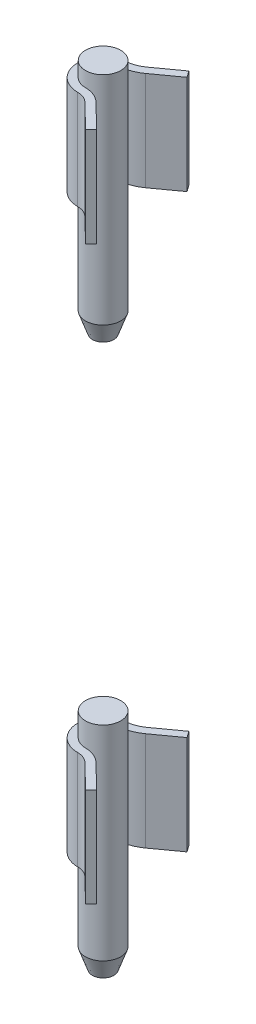
SolidWorks part; units mm, degrees
ref_plane "Front Plane" through (0, 0, 0) normal (0, 0, 1) x (1, 0, 0)
ref_plane "Top Plane" through (0, 0, 0) normal (0, 1, 0) x (1, 0, 0)
ref_plane "Right Plane" through (0, 0, 0) normal (1, 0, 0) x (0, 0, -1)
sketch "Sketch1" plane through (0, 0, 0) normal (0, 1, 0) x (1, 0, 0)
  circle A0 centre (0, 0) radius 4.5
  dimension "D1" = 9
extrude "Boss-Extrude1" add sketch "Sketch1" along normal blind 55
chamfer "Chamfer1" distance 1.75 distance2 5 1 edges at (0, 0, 4.5)
ref_plane "Plane1" through (0, 73, 0) normal (0, -1, 0) x (-1, 0, 0)
ref_plane "Plane2" through (0, 25.9, 0) normal (0, -1, 0) x (-1, 0, 0)
sketch "Sketch2" plane through (0, 25.9, 0) normal (0, -1, 0) x (-1, 0, 0)
  line L0 (-10.6679, -12.3261) -> (-4.5, -6.3274)
  line L2 (-9.2735, -13.7598) -> (-3.1056, -7.7611)
  line L4 (-9.2735, -13.7598) -> (-10.6679, -12.3261)
  line L7 (-3.3302, 7.9496) -> (-9.4981, 12.3976)
  line L8 (-9.4981, 12.3976) -> (-10.6679, 10.7754)
  line L9 (-10.6679, 10.7754) -> (-4.5, 6.3274)
  line L10 (-4.5, 6.3274) -> (-4.5, -6.3274) construction
  line L11 (0, 0) -> (-4.5, 0) construction
  arc A0 (-4.5, -6.3274) -> (0, -4.5) centre (0, -10.9544) cw
  arc A1 (0, -4.5) -> (0.4201, 4.4804) centre (0, 0) ccw
  arc A3 (-3.1056, -7.7611) -> (0, -6.5) centre (0, -10.9544) cw
  arc A4 (0, -6.5) -> (0.6068, 6.4716) centre (0, 0) ccw
  circle A6 centre (0, 0) radius 4.5 construction
  arc A7 (0.6068, 6.4716) -> (-3.3302, 7.9496) centre (1.3544, 14.4456) cw
  arc A8 (-4.5, 6.3274) -> (0.4201, 4.4804) centre (1.3544, 14.4456) ccw
  point P22 (-4.5, 0)
  dimension "D1" = 2
  dimension "D2" = 80
extrude "Boss-Extrude2" add sketch "Sketch2" against normal blind 25.3
pattern_linear "LPattern1" count 2 spacing 146.1 along (0, 1, 0) of bodies 103 101
sketch "Sketch3" plane through (0, 0, 0) normal (1, 0, 0) x (0, 0, -1)
  line L0 (0, 146.1) -> (0, 140.7)
  line L2 (-4.5, 151.1) -> (-4.5, 145.7)
  line L3 (-4.5, 145.7) -> (-2.75, 140.7)
  line L4 (-2.75, 140.7) -> (0, 140.7)
  line L8 (-4.5, 151.1) -> (-2.75, 146.1) construction
  line L11 (-4.5, 151.1) -> (-2.75, 146.1)
  line L13 (10.7754, 172) -> (6.3274, 172) construction
  line L14 (-2.75, 146.1) -> (0, 146.1)
  dimension "D1" = 31.3
revolve "Revolve3" add sketch "Sketch3" angle 360 about L0
sketch "Sketch4" plane through (0, 55, 0) normal (0, 1, 0) x (1, 0, 0)
  circle A1 centre (0, 0) radius 4.5
  circle A2 centre (0, 0) radius 4.5
  dimension "D1" = 0
extrude "Boss-Extrude3" add sketch "Sketch4" along normal blind 2.2
